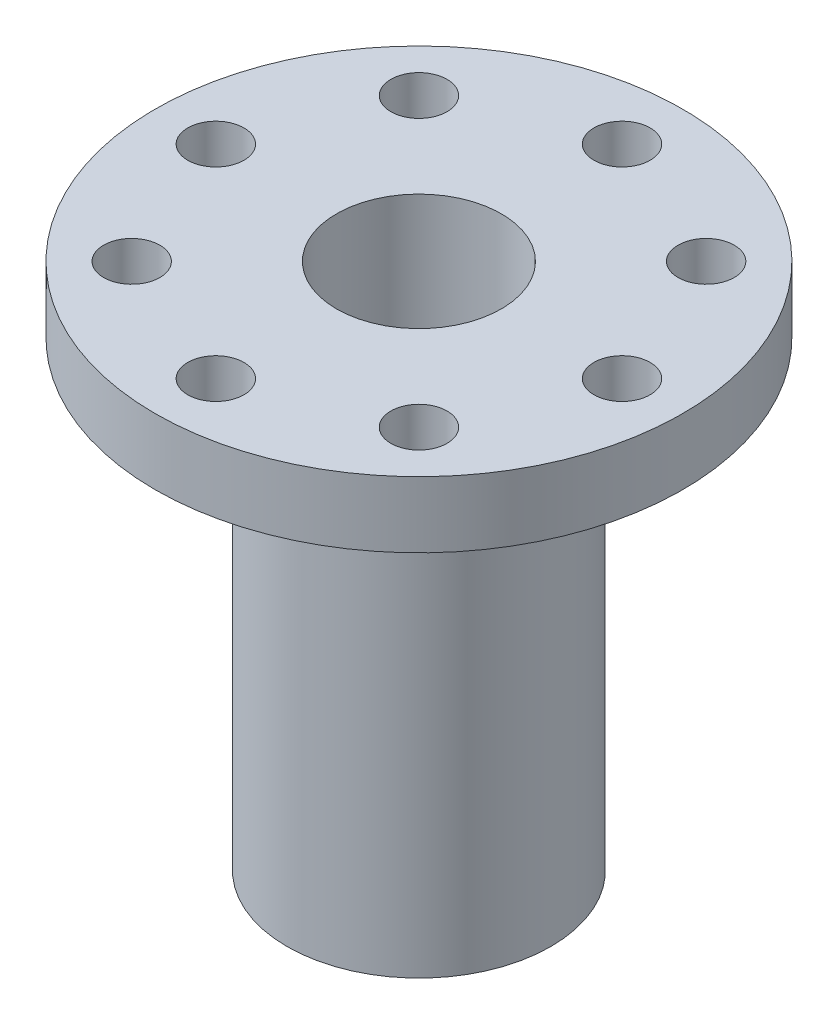
SolidWorks part; units mm, degrees
material "6061 Alloy"
ref_plane "Front Plane" through (0, 0, 0) normal (0, 0, 1) x (1, 0, 0)
ref_plane "Top Plane" through (0, 0, 0) normal (0, 1, 0) x (1, 0, 0)
ref_plane "Right Plane" through (0, 0, 0) normal (1, 0, 0) x (0, 0, -1)
sketch "Sketch1" plane through (0, 0, 0) normal (0, 1, 0) x (1, 0, 0)
  circle A0 centre (0, 0) radius 12.7
  dimension "D1" = 25.4
extrude "Boss-Extrude1" add sketch "Sketch1" along normal blind 3.175
sketch "Sketch2" plane through (0, 0, 0) normal (0, 1, 0) x (1, 0, 0)
  circle A0 centre (0, 0) radius 6.35
  dimension "D1" = 12.7
extrude "Boss-Extrude2" add sketch "Sketch2" against normal blind 22.225
sketch "Sketch3" plane through (0, -22.225, 0) normal (0, -1, 0) x (1, 0, 0)
  circle A0 centre (0, 0) radius 3
  dimension "D1" = 6
extrude "Cut-Extrude1" cut sketch "Sketch3" against normal blind 3.175
sketch "Sketch4" plane through (0, 3.175, 0) normal (0, 1, 0) x (1, 0, 0)
  circle A0 centre (0, 0) radius 3.9688
  dimension "D1" = 7.9375
extrude "Cut-Extrude2" cut sketch "Sketch4" against normal blind 19.05
sketch "Sketch5" plane through (0, -15.875, 0) normal (0, 1, 0) x (1, 0, 0)
  circle A0 centre (0, 0) radius 1.6
  dimension "D1" = 3.2
extrude "Cut-Extrude3" cut sketch "Sketch5" against normal up to next
hole_wizard "#6-32 Tapped Hole1" positions "Sketch7" profile "Sketch6" tap size "#6-32" standard "Ansi Inch" end condition up to next
sketch "Sketch7" plane through (0, 3.175, 0) normal (0, 1, 0) x (-1, 0, 0)
  point P0 (0, -9.779)
  point P8 (-6.9148, -6.9148)
  point P9 (-9.779, 0)
  point P10 (-6.9148, 6.9148)
  point P11 (0, 9.779)
  point P12 (6.9148, 6.9148)
  point P13 (9.779, 0)
  point P14 (6.9148, -6.9148)
  dimension "D1" = 9.779
  dimension "D2" = 8
sketch "Sketch6" plane through (0, 3.175, -9.779) normal (1, 0, 0) x (0, 0, 1)
  line L0 (0, 0) -> (0, 3.175)
  line L1 (0, 3.175) -> (1.3525, 3.175)
  line L2 (1.3525, 3.175) -> (1.3525, 0)
  line L5 (1.3525, 0) -> (0, 0)
  line L11 (0, -6.35) -> (0, 107.95) construction
  dimension "Thread Major Dia." = 2.7051
  dimension "Thru Tap Drill Depth" = 3.175
